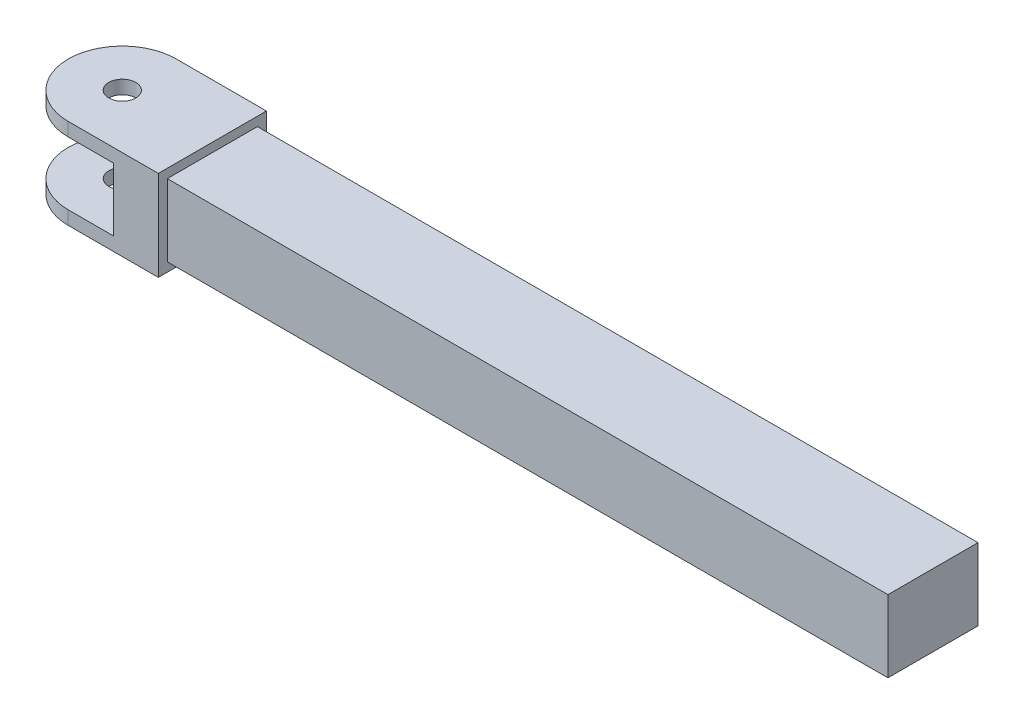
SolidWorks part; units mm, degrees
ref_plane "Płaszczyzna przednia" through (0, 0, 0) normal (0, 0, 1) x (1, 0, 0)
ref_plane "Płaszczyzna górna" through (0, 0, 0) normal (0, 1, 0) x (1, 0, 0)
ref_plane "Płaszczyzna prawa" through (0, 0, 0) normal (1, 0, 0) x (0, 0, -1)
sketch "Szkic1" plane through (0, 0, 0) normal (0, 1, 0) x (1, 0, 0)
  line L0 (90, 6) -> (90, -6)
  line L1 (0, 6) -> (90, 6)
  line L2 (0, -6) -> (90, -6)
  circle A0 centre (0, 0) radius 1.5
  arc A1 (0, 6) -> (0, -6) centre (0, 0) ccw
  point P3 (37.5, 0)
  dimension "D1" = 3
  dimension "D2" = 6
  dimension "D3" = 90
extrude "Dodanie-wyciągnięcie1" add sketch "Szkic1" along normal blind 10
sketch "Szkic2" plane through (0, 0, -6) normal (0, 0, -1) x (-1, 0, 0)
  line L8 (-5, 8.5) -> (17, 8.5)
  line L9 (-5, 8.5) -> (-5, 1.5)
  line L10 (-5, 1.5) -> (17, 1.5)
  line L11 (17, 8.5) -> (17, 1.5)
  line L12 (-5, 8.5) -> (17, 1.5) construction
  line L13 (-5, 1.5) -> (17, 8.5) construction
  line L14 (6, 0) -> (6, 10) construction
  point P7 (6, 5)
  dimension "D3" = 22
  dimension "D4" = 7
  dimension "D5" = 8.5
extrude "Wytnij-wyciągnięcie1" cut sketch "Szkic2" against normal through all
sketch "Szkic3" plane through (90, 0, 0) normal (1, 0, 0) x (0, 0, -1)
  line L8 (-5, 1) -> (5, 1)
  line L9 (5, 1) -> (5, 9)
  line L10 (5, 9) -> (-5, 9)
  line L11 (-5, 9) -> (-5, 1)
  line L12 (-5, 1) -> (5, 1)
  line L13 (5, 1) -> (5, 9)
  line L14 (5, 9) -> (-5, 9)
  line L15 (-5, 9) -> (-5, 1)
  dimension "D1" = 1
extrude "Wytnij-wyciągnięcie2" cut sketch "Szkic3" against normal blind 80 flip side to cut
